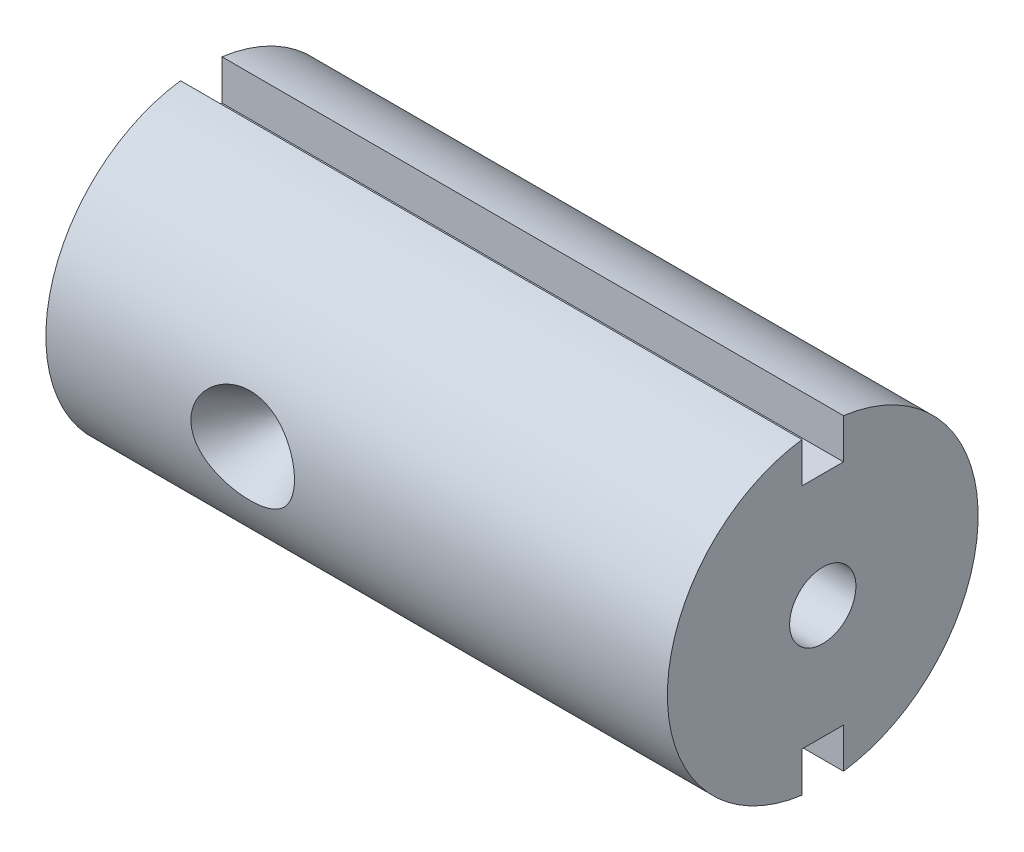
SolidWorks part; units mm, degrees
ref_plane "Plan de face" through (0, 0, 0) normal (0, 0, 1) x (1, 0, 0)
ref_plane "Plan de dessus" through (0, 0, 0) normal (0, 1, 0) x (1, 0, 0)
ref_plane "Plan de droite" through (0, 0, 0) normal (1, 0, 0) x (0, 0, -1)
sketch "Esquisse1" plane through (0, 0, 0) normal (1, 0, 0) x (0, 0, -1)
  circle A0 centre (0, 0) radius 7.5
  dimension "D1" = 15
extrude "Boss.-Extru.1" add sketch "Esquisse1" along normal blind 30
ref_plane "Plan1" through (0, 0, 7.5) normal (0, 0, 1) x (1, 0, 0)
sketch "Esquisse3" plane through (0, 0, 7.5) normal (0, 0, 1) x (1, 0, 0)
  line L0 (0, 7.5) -> (0, -7.5) construction
  circle A0 centre (9.5, 0) radius 2.5
  dimension "D1" = 5
  dimension "D2" = 9.5
extrude "Enlèv. mat.-Extru.1" cut sketch "Esquisse3" against normal blind 5.9 draft 30
sketch "Esquisse4" plane through (0, 0, 0) normal (-1, 0, 0) x (0, 0, 1)
  circle A0 centre (0, 0) radius 1.6
  dimension "D1" = 3.2
extrude "Enlèv. mat.-Extru.2" cut sketch "Esquisse4" against normal through all
sketch "Esquisse5" plane through (30, 0, 0) normal (1, 0, 0) x (0, 0, -1)
  line L0 (1, 8.1862) -> (1, 5.5)
  line L1 (-1, -8.1862) -> (1, -8.1862)
  line L2 (-1, -8.1862) -> (-1, -5.5)
  line L3 (-1, -5.5) -> (1, -5.5)
  line L4 (1, -8.1862) -> (1, -5.5)
  line L5 (1, 8.1862) -> (-1, 8.1862)
  line L6 (-1, 8.1862) -> (-1, 5.5)
  line L7 (1, 5.5) -> (-1, 5.5)
  circle A0 centre (0, 0) radius 7.5 construction
  point P12 (0, 0)
  dimension "D1" = 5.5
  dimension "D2" = 2
  dimension "D3" = 1
  dimension "D4" = 2
extrude "Enlèv. mat.-Extru.3" cut sketch "Esquisse5" against normal through all
